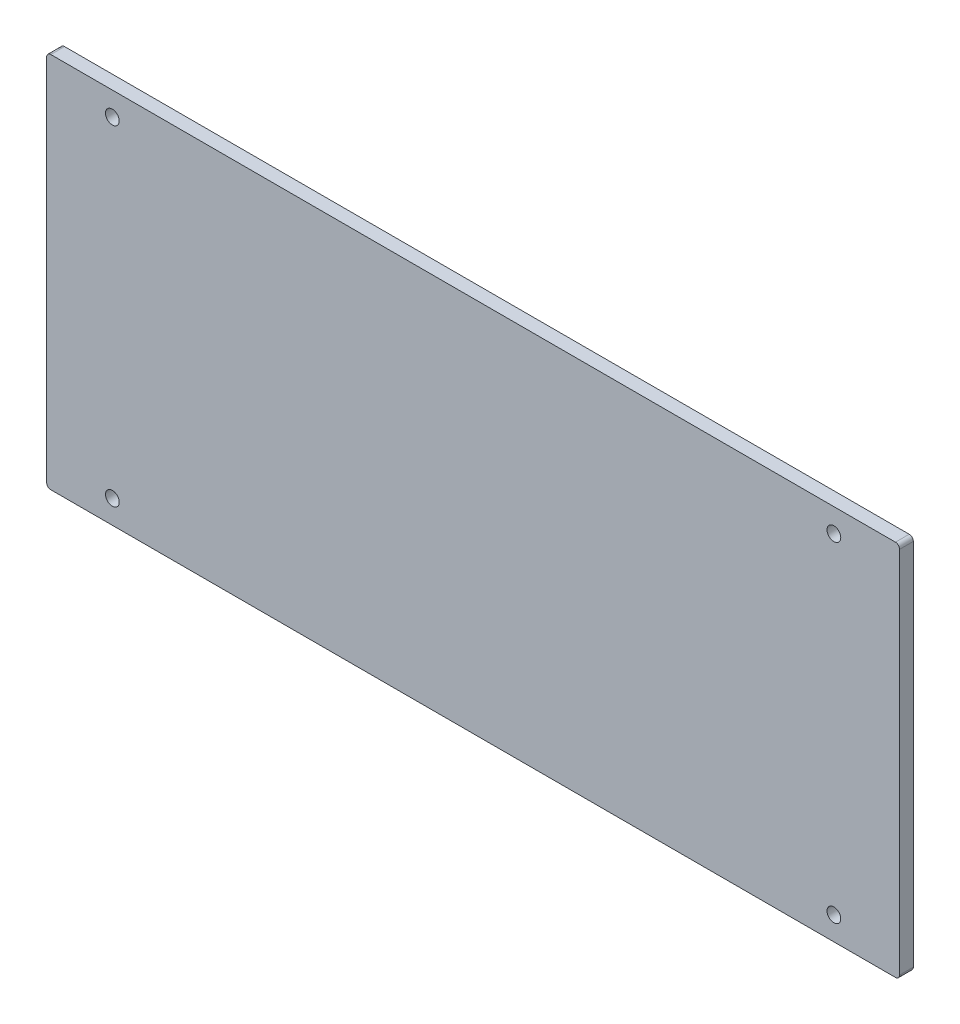
SolidWorks part; units mm, degrees
material "Alliage 1060"
ref_plane "Plan de face" through (0, 0, 0) normal (0, 0, 1) x (1, 0, 0)
ref_plane "Plan de dessus" through (0, 0, 0) normal (0, 1, 0) x (1, 0, 0)
ref_plane "Plan de droite" through (0, 0, 0) normal (1, 0, 0) x (0, 0, -1)
sketch "Esquisse1" plane through (0, 0, 0) normal (0, 0, 1) x (1, 0, 0)
  line L1 (-153.5, -68.5) -> (153.5, -68.5)
  line L2 (-155, -67) -> (-155, 67)
  line L3 (-153.5, 68.5) -> (153.5, 68.5)
  line L4 (155, -67) -> (155, 67)
  line L5 (-155, -68.5) -> (155, 68.5) construction
  line L6 (-155, 68.5) -> (155, -68.5) construction
  arc A0 (-153.5, -68.5) -> (-155, -67) centre (-153.5, -67) cw
  arc A1 (153.5, -68.5) -> (155, -67) centre (153.5, -67) ccw
  arc A2 (153.5, 68.5) -> (155, 67) centre (153.5, 67) cw
  arc A3 (-155, 67) -> (-153.5, 68.5) centre (-153.5, 67) cw
  point P0 (0, 0)
  dimension "D3" = 1.5
  dimension "D1" = 310
  dimension "D2" = 137
extrude "Boss.-Extru.1" add sketch "Esquisse1" along normal blind 5
ref_plane "Plan1" through (0, 0, 0) normal (0, -1, 0) x (-1, 0, 0)
sketch "Esquisse2" plane through (0, 0, 0) normal (0, 0, -1) x (-1, 0, 0)
  line L0 (-131.1192, -70) -> (-131.1192, -50) construction
  line L1 (-150, -70) -> (150, -70) construction
  line L2 (-155, 0) -> (155, 0) construction
  line L3 (-155, -67) -> (-155, 67) construction
  line L4 (155, 67) -> (155, -67) construction
  line L5 (0, 0) -> (0, 70) construction
  line L6 (-150, 70) -> (150, 70) construction
  circle A0 centre (-131.1192, -60) radius 2.5
  circle A1 centre (-131.1192, 60) radius 2.5
  circle A2 centre (131.1192, 60) radius 2.5
  circle A3 centre (131.1192, -60) radius 2.5
  dimension "D1" = 20
extrude "Enlèv. mat.-Extru.1" cut sketch "Esquisse2" against normal blind 5
